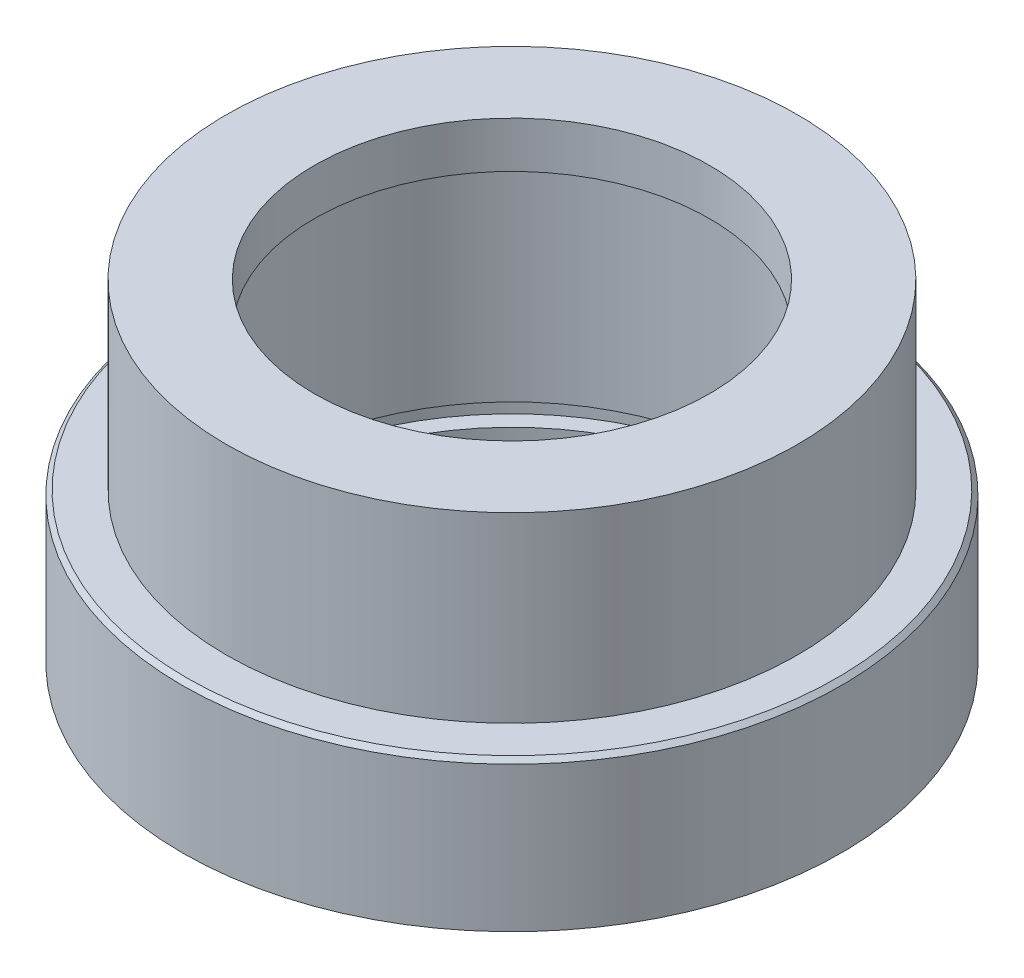
SolidWorks part; units mm, degrees
material "Alloy Steel"
ref_plane "Front Plane" through (0, 0, 0) normal (0, 0, 1) x (1, 0, 0)
ref_plane "Top Plane" through (0, 0, 0) normal (0, 1, 0) x (1, 0, 0)
ref_plane "Right Plane" through (0, 0, 0) normal (1, 0, 0) x (0, 0, -1)
sketch "Sketch1" plane through (0, 0, 0) normal (0, 0, 1) x (1, 0, 0)
  line L0 (0, 0) -> (0, -9480.2667) construction
  line L1 (-9, 7.35) -> (-13, 7.35)
  line L2 (-13, 7.35) -> (-13, -0.95)
  line L3 (-13, -0.95) -> (-14.8, -0.95)
  line L4 (-15, -1.15) -> (-15, -7.75)
  line L5 (-15, -7.75) -> (-11, -7.75)
  line L6 (-11, -7.75) -> (-11, -6.25)
  line L7 (-11, 5.25) -> (-9, 5.25)
  line L8 (-9, 5.25) -> (-9, 7.35)
  line L9 (-11, -5.25) -> (-11, 5.25)
  line L10 (-11, -5.25) -> (-11.75, -5.25)
  line L12 (-11, -6.25) -> (-11.75, -6.25)
  line L13 (-11.75, -5.25) -> (-11.75, -6.25)
  line L14 (-11, 0) -> (0, 0) construction
  line L15 (-14.8, -0.95) -> (-15, -1.15)
  point P7 (-15, -0.95)
  dimension "D1" = 1
  dimension "D2" = 10.5
  dimension "D3" = 6.8
  dimension "D4" = 8.3
  dimension "D5" = 30
  dimension "D6" = 26
  dimension "D7" = 18
  dimension "D8" = 23.5
  dimension "D9" = 22
  dimension "D10" = 1.5
revolve "Revolve1" add sketch "Sketch1" angle 360 about L0
